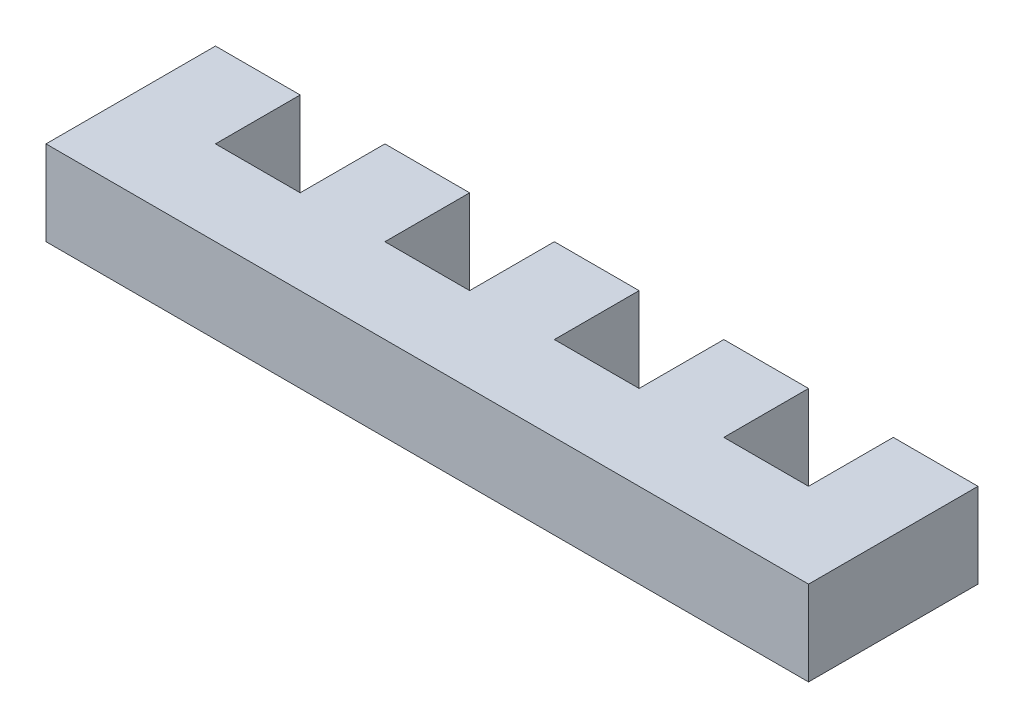
SolidWorks part; units mm, degrees
ref_plane "Front Plane" through (0, 0, 0) normal (0, 0, 1) x (1, 0, 0)
ref_plane "Top Plane" through (0, 0, 0) normal (0, 1, 0) x (1, 0, 0)
ref_plane "Right Plane" through (0, 0, 0) normal (1, 0, 0) x (0, 0, -1)
sketch "Sketch1" plane through (0, 0, 0) normal (0, 1, 0) x (1, 0, 0)
  line L1 (0, 0) -> (57.15, 0)
  line L2 (0, 0) -> (0, 12.7)
  line L3 (0, 12.7) -> (57.15, 12.7)
  line L4 (57.15, 0) -> (57.15, 12.7)
  line L5 (6.35, 12.7) -> (12.7, 12.7)
  line L6 (6.35, 12.7) -> (6.35, 6.35)
  line L7 (6.35, 6.35) -> (12.7, 6.35)
  line L8 (12.7, 12.7) -> (12.7, 6.35)
  line L9 (19.05, 12.7) -> (25.4, 12.7)
  line L10 (19.05, 12.7) -> (19.05, 6.35)
  line L11 (19.05, 6.35) -> (25.4, 6.35)
  line L12 (25.4, 12.7) -> (25.4, 6.35)
  line L13 (31.75, 12.7) -> (38.1, 12.7)
  line L14 (31.75, 12.7) -> (31.75, 6.35)
  line L15 (31.75, 6.35) -> (38.1, 6.35)
  line L16 (38.1, 12.7) -> (38.1, 6.35)
  line L17 (44.45, 12.7) -> (50.8, 12.7)
  line L18 (44.45, 12.7) -> (44.45, 6.35)
  line L19 (44.45, 6.35) -> (50.8, 6.35)
  line L20 (50.8, 12.7) -> (50.8, 6.35)
  dimension "D1" = 12.7
  dimension "D2" = 57.15
  dimension "D3" = 6.35
  dimension "D4" = 6.35
  dimension "D5" = 6.35
  dimension "D6" = 6.35
  dimension "D7" = 6.35
  dimension "D8" = 6.35
  dimension "D9" = 6.35
  dimension "D10" = 6.35
  dimension "D11" = 6.35
  dimension "D12" = 6.35
  dimension "D13" = 6.35
  dimension "D14" = 6.35
extrude "Boss-Extrude1" add sketch "Sketch1" along normal blind 6.35 contours L3 L20 L19 L18 L16 L15 L14 L12 L11 L10 L8 L7 L6 L2 L1 L4
